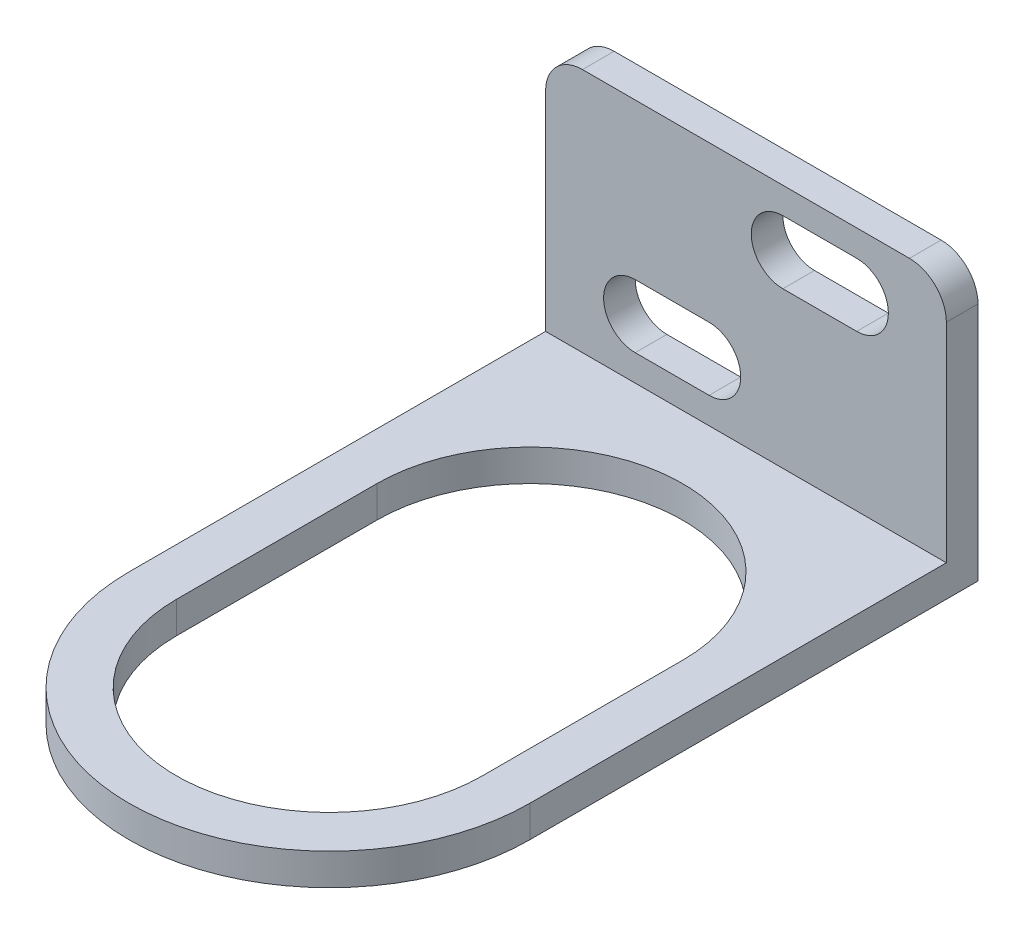
SolidWorks part; units mm, degrees
ref_plane "Front Plane" through (0, 0, 0) normal (0, 0, 1) x (1, 0, 0)
ref_plane "Top Plane" through (0, 0, 0) normal (0, 1, 0) x (1, 0, 0)
ref_plane "Right Plane" through (0, 0, 0) normal (1, 0, 0) x (0, 0, -1)
sketch "Sketch2" plane through (0, 0, 0) normal (1, 0, 0) x (0, 0, -1)
  line L0 (-63, 0) -> (0, 0)
  line L1 (0, 0) -> (0, 26.25)
  dimension "D1" = 63
  dimension "D2" = 26.25
extrude "Extrude-Thin1" add sketch "Sketch2" against normal blind 38 thin thin type one direction reverse wall 3
sketch "Sketch3" plane through (0, 0, 3) normal (0, 0, 1) x (1, 0, 0)
  line L0 (-29.5, 8.5) -> (-22.5, 8.5) construction
  line L1 (-29.5, 11.5) -> (-22.5, 11.5)
  line L2 (-29.5, 5.5) -> (-22.5, 5.5)
  line L3 (-15.5, 20.75) -> (-8.5, 20.75) construction
  line L4 (-15.5, 23.75) -> (-8.5, 23.75)
  line L5 (-15.5, 17.75) -> (-8.5, 17.75)
  line L6 (-38, 3) -> (0, 3) construction
  line L7 (-38, 3) -> (-38, 26.25) construction
  line L9 (0, 3) -> (0, 26.25) construction
  line L11 (-38, 26.25) -> (0, 26.25) construction
  arc A0 (-29.5, 11.5) -> (-29.5, 5.5) centre (-29.5, 8.5) ccw
  arc A1 (-22.5, 5.5) -> (-22.5, 11.5) centre (-22.5, 8.5) ccw
  arc A2 (-15.5, 23.75) -> (-15.5, 17.75) centre (-15.5, 20.75) ccw
  arc A3 (-8.5, 17.75) -> (-8.5, 23.75) centre (-8.5, 20.75) ccw
  point P2 (-26, 8.5)
  point P7 (-12, 20.75)
  dimension "D1" = 7
  dimension "D2" = 6
  dimension "D3" = 5.5
  dimension "D4" = 12
  dimension "D5" = 12
  dimension "D6" = 5.5
extrude "Cut-Extrude1" cut sketch "Sketch3" against normal through all
fillet "Fillet1" radius 3.5 1 edges at (-38, 26.25, 1.5)
fillet "Fillet2" radius 3.5 1 edges at (0, 26.25, 1.5)
sketch "Sketch4" plane through (0, 3, 0) normal (0, 1, 0) x (1, 0, 0)
  line L0 (-19, -23.5) -> (-19, -42.5) construction
  line L1 (-4.5, -23.5) -> (-4.5, -42.5)
  line L2 (-33.5, -23.5) -> (-33.5, -42.5)
  line L3 (-19, -33) -> (0, -33) construction
  line L4 (0, -63) -> (0, -3) construction
  line L5 (-38, -63) -> (0, -63) construction
  line L6 (0, -23.5) -> (0, -42.5)
  line L7 (-38, -23.5) -> (-38, -42.5)
  line L8 (-38, -63) -> (-38, -3) construction
  line L9 (0, -63) -> (0, -3)
  line L10 (-38, -63) -> (0, -63)
  line L11 (-38, -63) -> (-38, -3)
  arc A0 (-4.5, -23.5) -> (-33.5, -23.5) centre (-19, -23.5) ccw
  arc A1 (-33.5, -42.5) -> (-4.5, -42.5) centre (-19, -42.5) ccw
  arc A2 (-38, -42.5) -> (0, -42.5) centre (-19, -42.5) ccw
  arc A3 (0, -23.5) -> (-38, -23.5) centre (-19, -23.5) ccw
  point P2 (-19, -33)
  point P13 (-19, -63)
  line M7 (0, -63) -> (0, -3)
  line M9 (-38, -3) -> (-38, -63)
  line M10 (-38, -63) -> (0, -63)
  dimension "D1" = 29
  dimension "D2" = 19
  dimension "D3" = 4.5
extrude "Cut-Extrude2" cut sketch "Sketch4" against normal through all contours L2 A1 L1 A0 | A2 M9 M10 M7
